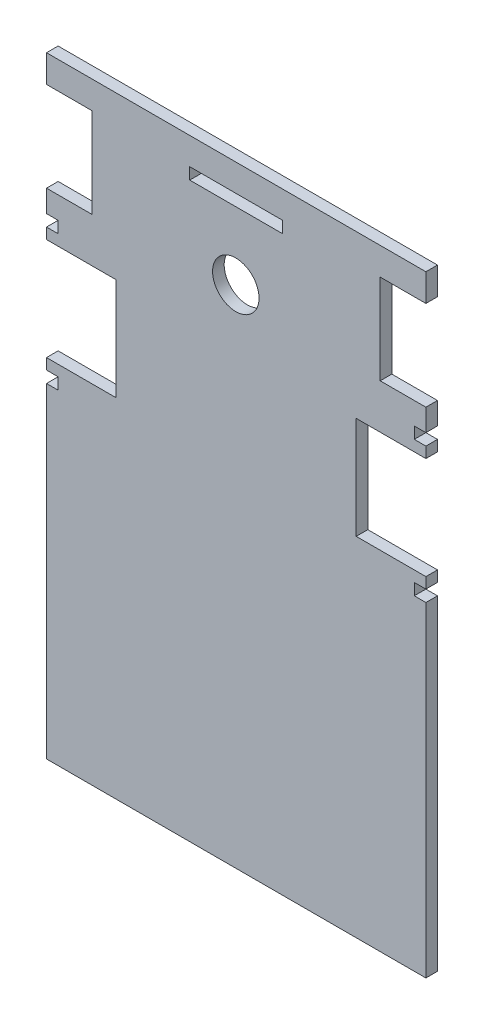
SolidWorks part; units mm, degrees
ref_plane "Alzado" through (0, 0, 0) normal (0, 0, 1) x (1, 0, 0)
ref_plane "Planta" through (0, 0, 0) normal (0, 1, 0) x (1, 0, 0)
ref_plane "Vista lateral" through (0, 0, 0) normal (1, 0, 0) x (0, 0, -1)
sketch "Model" plane through (0, 0, 0) normal (0, 0, 1) x (1, 0, 0)
  line L0 (11.3925, 93.1934) -> (11.3925, 86.0934)
  line L1 (109.3925, 86.0934) -> (109.3925, 93.1934)
  line L2 (97.5925, 86.0934) -> (109.3925, 86.0934)
  line L3 (97.5925, 62.8934) -> (97.5925, 86.0934)
  line L4 (109.3925, 62.8934) -> (97.5925, 62.8934)
  line L5 (109.3925, -64.8066) -> (109.3925, 19.1934)
  line L6 (11.3925, -64.8066) -> (109.3925, -64.8066)
  line L7 (11.3925, 19.1934) -> (11.3925, -64.8066)
  line L8 (109.3925, 93.1934) -> (11.3925, 93.1934)
  line L9 (23.1925, 62.8934) -> (11.3925, 62.8934)
  line L10 (23.1925, 86.0934) -> (23.1925, 62.8934)
  line L11 (11.3925, 86.0934) -> (23.1925, 86.0934)
  line L12 (48.3925, 83.1934) -> (72.3925, 83.1934)
  line L13 (48.3925, 86.1934) -> (48.3925, 83.1934)
  line L14 (72.3925, 86.1934) -> (48.3925, 86.1934)
  line L15 (72.3925, 83.1934) -> (72.3925, 86.1934)
  line L40 (109.3925, 51.3934) -> (91.3925, 51.3934)
  line L41 (11.3925, 51.3934) -> (29.3925, 51.3934)
  line L42 (91.3925, 51.3934) -> (91.3925, 24.9934)
  line L43 (29.3925, 51.3934) -> (29.3925, 24.9934)
  line L44 (29.3925, 24.9934) -> (11.3925, 24.9934)
  line L45 (91.3925, 24.9934) -> (109.3925, 24.9934)
  line L48 (11.3925, 62.8934) -> (11.3925, 57.1934)
  line L49 (109.3925, 62.8934) -> (109.3925, 57.1934)
  line L50 (106.3925, 54.1934) -> (106.3925, 57.1934)
  line L51 (106.3925, 19.1934) -> (106.3925, 22.1934)
  line L52 (14.3925, 54.1934) -> (14.3925, 57.1934)
  line L53 (14.3925, 19.1934) -> (14.3925, 22.1934)
  line L54 (106.3925, 22.1934) -> (109.3925, 22.1934)
  line L55 (106.3925, 57.1934) -> (109.3925, 57.1934)
  line L56 (14.3925, 57.1934) -> (11.3925, 57.1934)
  line L57 (14.3925, 22.1934) -> (11.3925, 22.1934)
  line L58 (106.3925, 19.1934) -> (109.3925, 19.1934)
  line L59 (106.3925, 54.1934) -> (109.3925, 54.1934)
  line L60 (14.3925, 54.1934) -> (11.3925, 54.1934)
  line L61 (14.3925, 19.1934) -> (11.3925, 19.1934)
  line L62 (109.3925, 54.1934) -> (109.3925, 51.3934)
  line L63 (109.3925, 22.1934) -> (109.3925, 24.9934)
  line L64 (11.3925, 22.1934) -> (11.3925, 24.9934)
  line L65 (11.3925, 54.1934) -> (11.3925, 51.3934)
  circle A0 centre (60.2918, 65.723) radius 6
extrude "Saliente-Extruir1" add sketch "Model" along normal blind 3
